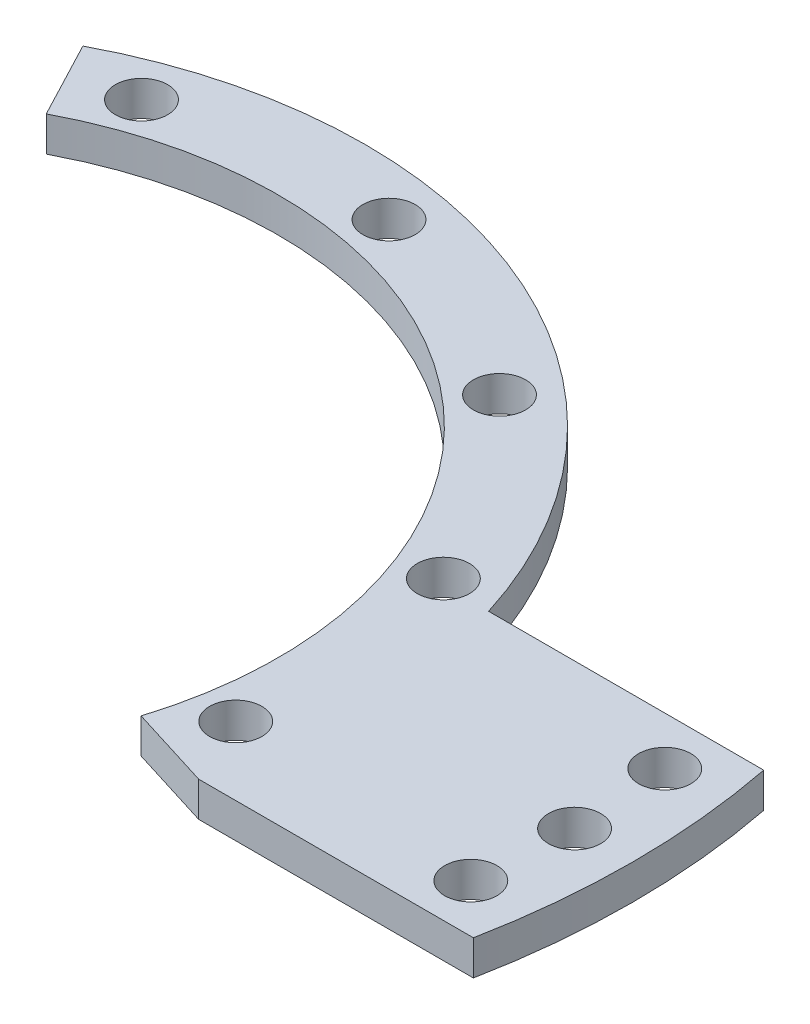
SolidWorks part; units mm, degrees
ref_plane "Front Plane" through (0, 0, 0) normal (0, 0, 1) x (1, 0, 0)
ref_plane "Top Plane" through (0, 0, 0) normal (0, 1, 0) x (1, 0, 0)
ref_plane "Right Plane" through (0, 0, 0) normal (1, 0, 0) x (0, 0, -1)
sketch "Sketch1" plane through (0, 0, 0) normal (0, 1, 0) x (1, 0, 0)
  circle A0 centre (0, 0) radius 42
  dimension "D1" = 84
extrude "Boss-Extrude1" add sketch "Sketch1" along normal blind 3
sketch "Sketch2" plane through (0, 0, 0) normal (0, 1, 0) x (1, 0, 0)
  line L0 (0, 0) -> (35, 0) construction
  line L1 (70, 12.5) -> (0, 12.5)
  line L2 (70, 12.5) -> (70, -12.5)
  line L3 (0, 12.5) -> (0, -12.5)
  line L4 (70, -12.5) -> (0, -12.5)
  line L5 (0, 0) -> (70, 0) construction
  line L6 (35, 12.5) -> (35, -12.5) construction
  dimension "D1" = 25
  dimension "D2" = 70
extrude "Boss-Extrude2" add sketch "Sketch2" along normal blind 3
sketch "Sketch3" plane through (0, 3, 0) normal (0, 1, 0) x (1, 0, 0)
  circle A0 centre (0, 0) radius 34.5
  dimension "D1" = 69
extrude "Cut-Extrude1" cut sketch "Sketch3" against normal through all both and the other way through all
sketch "Sketch4" plane through (0, 3, 0) normal (0, 1, 0) x (1, 0, 0)
  line L0 (0, 0) -> (70, 0) construction
  line L1 (70, -12.5) -> (70, 12.5) construction
  line L2 (0, 0) -> (40.1, -12.4897)
  line L3 (-19.5234, 37.1865) -> (0, 0)
  arc A0 (40.0968, 12.5) -> (40.0968, -12.5) centre (0, 0) ccw construction
  arc A1 (40.1, -12.4897) -> (-19.5234, 37.1865) centre (0, 0) cw
  dimension "D1" = 225
  dimension "D2" = 17.3
extrude "Cut-Extrude2" cut sketch "Sketch4" against normal through all both and the other way through all
sketch "Sketch5" plane through (0, 3, 0) normal (0, 1, 0) x (1, 0, 0)
  line L0 (0, 0) -> (0, 42) construction
  line L1 (0, 0) -> (-12.9968, 35.7083) construction
  circle A0 centre (0, 0) radius 38 construction
  arc A2 (40.0968, 12.5) -> (-19.5234, 37.1865) centre (0, 0) ccw construction
  circle A3 centre (-12.9968, 35.7083) radius 2.25
  dimension "D1" = 76
  dimension "D2" = 4.5
  dimension "D3" = 20
extrude "Cut-Extrude3" cut sketch "Sketch5" against normal through all both and the other way through all
pattern_circular "CirPattern1" count 12 over 360 of "Cut-Extrude3"
sketch "Sketch6" plane through (0, 0, 0) normal (0, 1, 0) x (1, 0, 0)
  circle A0 centre (0, 0) radius 55 construction
  circle A1 centre (0, 0) radius 122.1838
  circle A2 centre (0, 0) radius 65
  dimension "D1" = 110
  dimension "D2" = 130
extrude "Cut-Extrude4" cut sketch "Sketch6" against normal through all both and the other way through all
sketch "Sketch7" plane through (0, 3, 0) normal (0, 1, 0) x (1, 0, 0)
  line L0 (0, 0) -> (60, 0) construction
  circle A0 centre (60, 0) radius 2.25
  dimension "D1" = 4.5
  dimension "D2" = 60
extrude "Cut-Extrude5" cut sketch "Sketch7" against normal through all both and the other way through all
pattern_circular "CirPattern2" count 2 every 8 about axis through (0, 3, 0) along (0, 1, 0) of "Cut-Extrude5"
